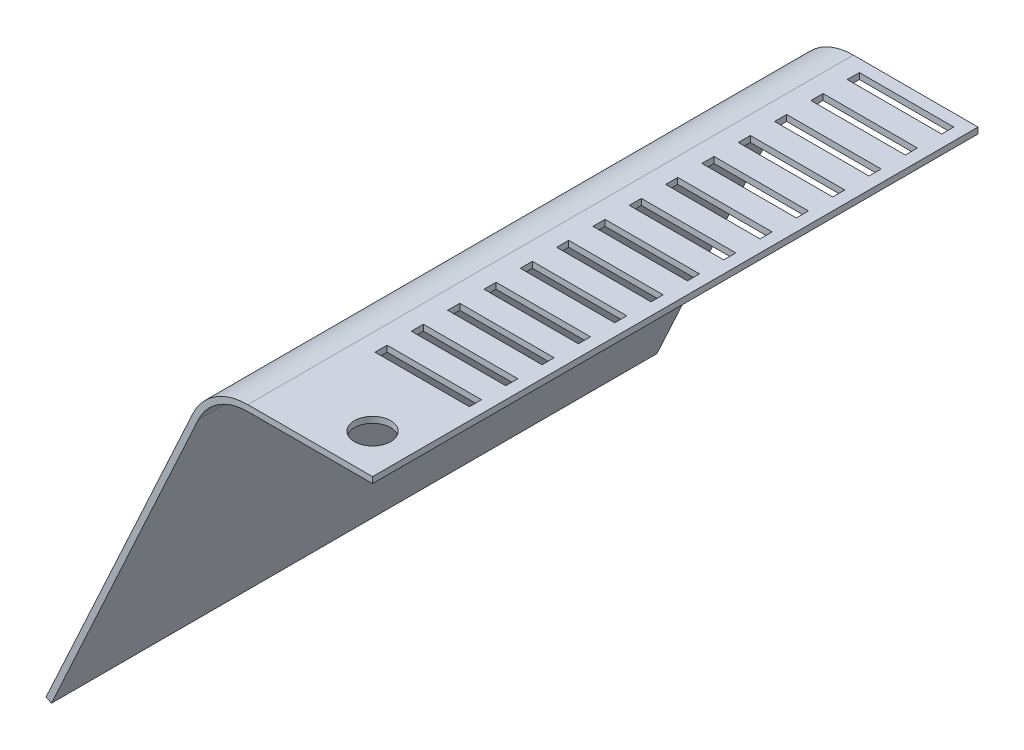
SolidWorks part; units mm, degrees
ref_plane "Front Plane" through (0, 0, 0) normal (0, 0, 1) x (1, 0, 0)
ref_plane "Top Plane" through (0, 0, 0) normal (0, 1, 0) x (1, 0, 0)
ref_plane "Right Plane" through (0, 0, 0) normal (1, 0, 0) x (0, 0, -1)
sketch "Sketch1" plane through (0, 0, 0) normal (0, 0, 1) x (1, 0, 0)
  line L0 (0, 0) -> (242.5468, 526.8501)
  line L1 (333.383, 585.0317) -> (539.333, 585.0317)
  arc A0 (242.5468, 526.8501) -> (333.383, 585.0317) centre (333.383, 485.0317) cw
  point P5 (333.383, 585.0317)
  dimension "D2" = 100
  dimension "D1" = 580
  dimension "D3" = 205.95
  dimension "D4" = 114.72
extrude "Extrude-Thin1" add sketch "Sketch1" along normal mid plane 1000 thin
sketch "Sketch2" plane through (0, 585.0317, 0) normal (0, 1, 0) x (1, 0, 0)
  line L0 (333.383, -500) -> (539.333, -500) construction
  line L1 (363.383, 480) -> (519.333, 480)
  line L2 (363.383, 480) -> (363.383, 460)
  line L3 (363.383, 460) -> (519.333, 460)
  line L4 (519.333, 480) -> (519.333, 460)
  line L5 (539.333, -500) -> (539.333, 500) construction
  line L6 (333.383, 500) -> (539.333, 500) construction
  line L7 (333.383, -500) -> (333.383, 500) construction
  line L8 (363.383, 420) -> (519.333, 420)
  line L9 (363.383, 420) -> (363.383, 400)
  line L10 (363.383, 400) -> (519.333, 400)
  line L11 (519.333, 420) -> (519.333, 400)
  line L12 (363.383, 360) -> (519.333, 360)
  line L13 (363.383, 360) -> (363.383, 340)
  line L14 (363.383, 340) -> (519.333, 340)
  line L15 (519.333, 360) -> (519.333, 340)
  line L16 (363.383, 300) -> (519.333, 300)
  line L17 (363.383, 300) -> (363.383, 280)
  line L18 (363.383, 280) -> (519.333, 280)
  line L19 (519.333, 300) -> (519.333, 280)
  line L20 (363.383, 240) -> (519.333, 240)
  line L21 (363.383, 240) -> (363.383, 220)
  line L22 (363.383, 220) -> (519.333, 220)
  line L23 (519.333, 240) -> (519.333, 220)
  line L24 (363.383, 180) -> (519.333, 180)
  line L25 (363.383, 180) -> (363.383, 160)
  line L26 (363.383, 160) -> (519.333, 160)
  line L27 (519.333, 180) -> (519.333, 160)
  line L28 (363.383, 120) -> (519.333, 120)
  line L29 (363.383, 120) -> (363.383, 100)
  line L30 (363.383, 100) -> (519.333, 100)
  line L31 (519.333, 120) -> (519.333, 100)
  line L32 (363.383, 60) -> (519.333, 60)
  line L33 (363.383, 60) -> (363.383, 40)
  line L34 (363.383, 40) -> (519.333, 40)
  line L35 (519.333, 60) -> (519.333, 40)
  line L36 (363.383, 0) -> (519.333, 0)
  line L37 (363.383, 0) -> (363.383, -20)
  line L38 (363.383, -20) -> (519.333, -20)
  line L39 (519.333, 0) -> (519.333, -20)
  line L40 (363.383, -60) -> (519.333, -60)
  line L41 (363.383, -60) -> (363.383, -80)
  line L42 (363.383, -80) -> (519.333, -80)
  line L43 (519.333, -60) -> (519.333, -80)
  line L44 (363.383, -120) -> (519.333, -120)
  line L45 (363.383, -120) -> (363.383, -140)
  line L46 (363.383, -140) -> (519.333, -140)
  line L47 (519.333, -120) -> (519.333, -140)
  line L48 (363.383, -180) -> (519.333, -180)
  line L49 (363.383, -180) -> (363.383, -200)
  line L50 (363.383, -200) -> (519.333, -200)
  line L51 (519.333, -180) -> (519.333, -200)
  line L52 (363.383, -240) -> (519.333, -240)
  line L53 (363.383, -240) -> (363.383, -260)
  line L54 (363.383, -260) -> (519.333, -260)
  line L55 (519.333, -240) -> (519.333, -260)
  line L56 (363.383, -300) -> (519.333, -300)
  line L57 (363.383, -300) -> (363.383, -320)
  line L58 (363.383, -320) -> (519.333, -320)
  line L59 (519.333, -300) -> (519.333, -320)
  circle A0 centre (474.333, -435) radius 30
  dimension "D3" = 60
  dimension "D1" = 65
  dimension "D2" = 65
  dimension "D4" = 20
  dimension "D5" = 20
  dimension "D6" = 30
  dimension "D7" = 20
  dimension "D8" = 14
extrude "Cut-Extrude1" cut sketch "Sketch2" against normal through all
